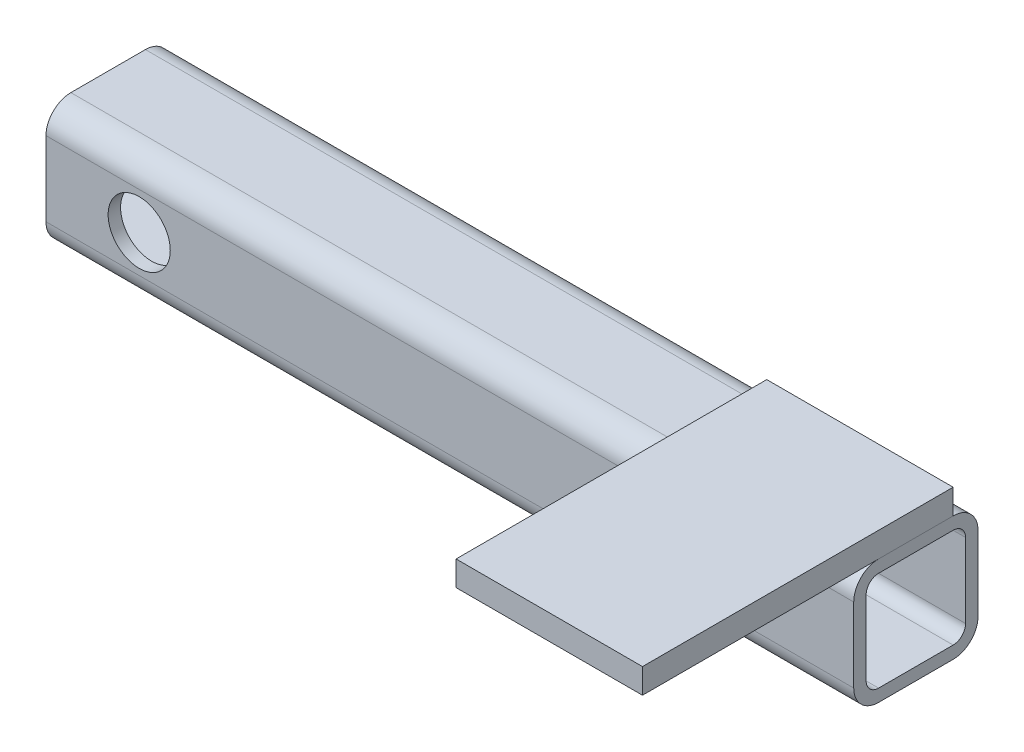
SolidWorks part; units mm, degrees
ref_plane "Front Plane" through (0, 0, 0) normal (0, 0, 1) x (1, 0, 0)
ref_plane "Top Plane" through (0, 0, 0) normal (0, 1, 0) x (1, 0, 0)
ref_plane "Right Plane" through (0, 0, 0) normal (1, 0, 0) x (0, 0, -1)
sketch "Sketch1" plane through (0, 0, 0) normal (0, 0, 1) x (1, 0, 0)
  line L0 (0, 0) -> (130, 0)
  dimension "D1" = 130
other "Structural Member1"
ref_plane "Plane1" through (0, 0, 0) normal (1, 0, 0) x (0, 1, 0)
sketch "Sketch11" plane through (0, 0, 0) normal (1, 0, 0) x (0, 1, 0)
  line L0 (-6, -8) -> (6, -8)
  line L1 (-8, -6) -> (-8, 6)
  line L2 (6, 8) -> (-6, 8)
  line L3 (8, 6) -> (8, -6)
  line L4 (-6, -10) -> (6, -10)
  line L5 (-10, -6) -> (-10, 6)
  line L6 (6, 10) -> (-6, 10)
  line L7 (10, 6) -> (10, -6)
  arc A0 (10, 6) -> (6, 10) centre (6, 6) ccw
  arc A1 (6, -10) -> (10, -6) centre (6, -6) ccw
  arc A2 (-10, -6) -> (-6, -10) centre (-6, -6) ccw
  arc A3 (-6, 10) -> (-10, 6) centre (-6, 6) ccw
  arc A4 (-6, 8) -> (-8, 6) centre (-6, 6) ccw
  arc A5 (8, 6) -> (6, 8) centre (6, 6) ccw
  arc A6 (6, -8) -> (8, -6) centre (6, -6) ccw
  arc A7 (-8, -6) -> (-6, -8) centre (-6, -6) ccw
  point P0 (-10, 0)
  point P1 (10, 0)
  point P2 (0, 10)
  point P3 (0, -10)
  point P4 (0, 0)
  point P5 (-10, -10)
  point P6 (10, -10)
  point P7 (10, 10)
  point P8 (-10, 10)
  point P33 (0, 0)
  dimension "D1" = 4
  dimension "Thickness" = 2
  dimension "V_leg" = 20
sketch "Sketch12" plane through (0, 0, 10) normal (0, 0, 1) x (1, 0, 0)
  line L0 (0, 6) -> (0, -6) construction
  circle A0 centre (15, 0) radius 5
  dimension "D1" = 10
  dimension "D2" = 15
extrude "Cut-Extrude1" cut sketch "Sketch12" against normal blind 35 contours A0
sketch "Sketch13" plane through (0, 10, 0) normal (0, 1, 0) x (1, 0, 0)
  line L1 (130, 6) -> (100, 6)
  line L2 (130, 6) -> (130, -44)
  line L3 (130, -44) -> (100, -44)
  line L4 (100, 6) -> (100, -44)
  dimension "D1" = 50
  dimension "D2" = 30
extrude "Boss-Extrude1" add sketch "Sketch13" along normal blind 4 separate body contours L2 L3 L4 L1
